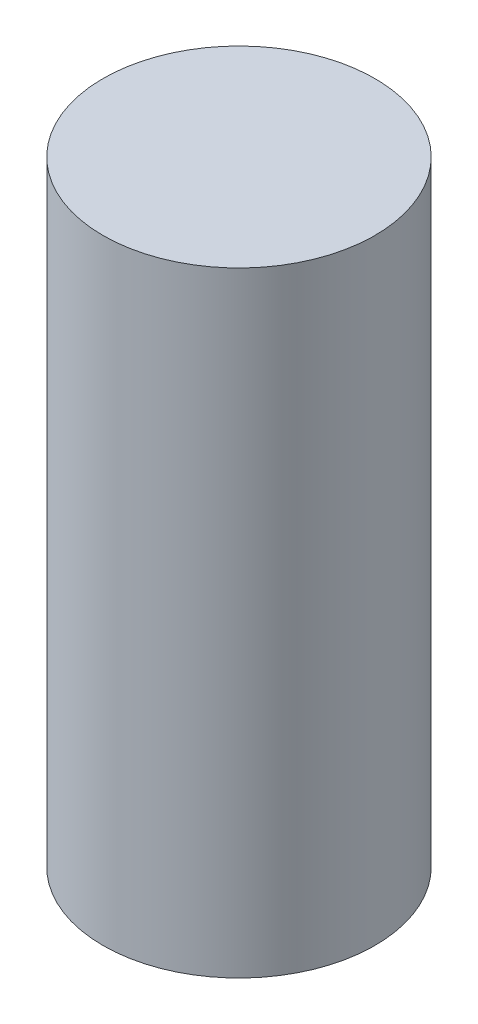
SolidWorks part; units mm, degrees
ref_plane "Front" through (0, 0, 0) normal (0, 0, 1) x (1, 0, 0)
ref_plane "Top" through (0, 0, 0) normal (0, 1, 0) x (1, 0, 0)
ref_plane "Right" through (0, 0, 0) normal (1, 0, 0) x (0, 0, -1)
sketch "Sketch1" plane through (0, 0, 0) normal (0, 1, 0) x (1, 0, 0)
  circle A0 centre (0, 0) radius 3.975
  dimension "D1" = 7.95
extrude "Boss-Extrude1" add sketch "Sketch1" along normal blind 17.98
